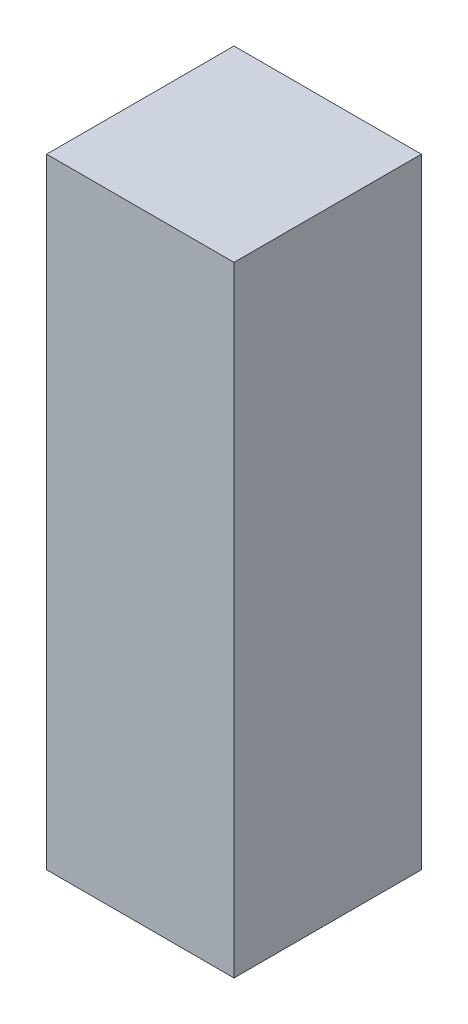
SolidWorks part; units mm, degrees
ref_plane "Plan de face" through (0, 0, 0) normal (0, 0, 1) x (1, 0, 0)
ref_plane "Plan de dessus" through (0, 0, 0) normal (0, 1, 0) x (1, 0, 0)
ref_plane "Plan de droite" through (0, 0, 0) normal (1, 0, 0) x (0, 0, -1)
sketch "Esquisse1" plane through (0, 0, 0) normal (0, 0, 1) x (1, 0, 0)
  line L1 (-17.8087, 7.8737) -> (-4.8087, 7.8737)
  line L2 (-17.8087, 7.8737) -> (-17.8087, -35.1263)
  line L3 (-17.8087, -35.1263) -> (-4.8087, -35.1263)
  line L4 (-4.8087, 7.8737) -> (-4.8087, -35.1263)
  dimension "D1" = 13
  dimension "D2" = 43
extrude "Boss.-Extru.1" add sketch "Esquisse1" along normal blind 13
